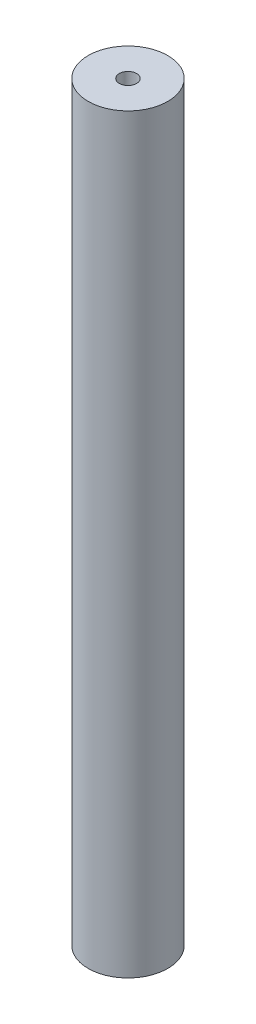
SolidWorks part; units mm, degrees
material "1060 Alloy"
ref_plane "Front Plane" through (0, 0, 0) normal (0, 0, 1) x (1, 0, 0)
ref_plane "Top Plane" through (0, 0, 0) normal (0, 1, 0) x (1, 0, 0)
ref_plane "Right Plane" through (0, 0, 0) normal (1, 0, 0) x (0, 0, -1)
sketch "Sketch1" plane through (0, 0, 0) normal (0, 1, 0) x (1, 0, 0)
  circle A0 centre (0, 0) radius 7.9375
  dimension "D1" = 15.875
extrude "Boss-Extrude1" add sketch "Sketch1" along normal blind 149.86
hole_wizard "#8-32 Tapped Hole3" positions "Sketch3" profile "Sketch2" tap size "#8-32" standard "ANSI Inch"
sketch "Sketch3" plane through (0, 0, 0) normal (0, -1, 0) x (-1, 0, 0)
  point P0 (0, 0)
sketch "Sketch2" plane through (0, 0, 0) normal (1, 0, 0) x (0, 0, -1)
  line L0 (0, 0) -> (0, 13.7378)
  line L1 (0, 13.7378) -> (1.7272, 12.7)
  line L2 (1.7272, 12.7) -> (1.7272, 0)
  line L5 (1.7272, 0) -> (0, 0)
  line L10 (0, 13.7378) -> (-1.7272, 12.7) construction
  line L11 (0, -6.35) -> (0, 107.95) construction
  dimension "Tap Drill Dia." = 3.4544
  dimension "Tap Drill Depth" = 12.7
  dimension "Drill Angle" = 118
cosmetic thread "Hole Thread1" parameters "D1"=12.7, "D2"=4.826
hole_wizard "#8-32 Tapped Hole4" positions "Sketch5" profile "Sketch4" tap size "#8-32" standard "ANSI Inch"
sketch "Sketch5" plane through (0, 149.86, 0) normal (0, 1, 0) x (1, 0, 0)
  point P0 (0, 0)
sketch "Sketch4" plane through (0, 149.86, 0) normal (1, 0, 0) x (0, 0, 1)
  line L0 (0, 0) -> (0, 13.7378)
  line L1 (0, 13.7378) -> (1.7272, 12.7)
  line L2 (1.7272, 12.7) -> (1.7272, 0)
  line L5 (1.7272, 0) -> (0, 0)
  line L10 (0, 13.7378) -> (-1.7272, 12.7) construction
  line L11 (0, -6.35) -> (0, 107.95) construction
  dimension "Tap Drill Dia." = 3.4544
  dimension "Tap Drill Depth" = 12.7
  dimension "Drill Angle" = 118
cosmetic thread "Hole Thread2" parameters "D1"=12.7, "D2"=4.826
